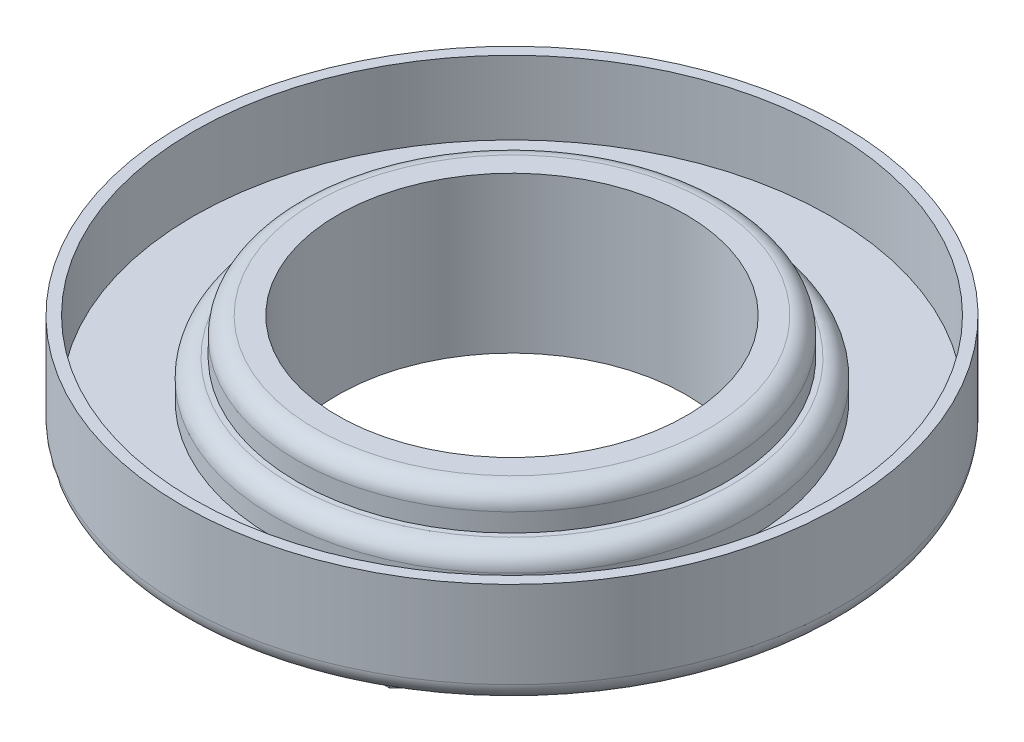
SolidWorks part; units mm, degrees
material "Zinc AC41A Alloy, As Cast"
ref_plane "Front Plane" through (0, 0, 0) normal (0, 0, 1) x (1, 0, 0)
ref_plane "Top Plane" through (0, 0, 0) normal (0, 1, 0) x (1, 0, 0)
ref_plane "Right Plane" through (0, 0, 0) normal (1, 0, 0) x (0, 0, -1)
sketch "Sketch1" plane through (0, 0, 0) normal (0, 1, 0) x (1, 0, 0)
  line L0 (0, 15.8115) -> (0, -15.8115) construction
  line L1 (-7.3398, 15.8115) -> (7.3398, 15.8115)
  line L2 (7.3398, 15.8115) -> (15.8115, 6.35)
  line L3 (15.8115, 6.35) -> (15.8115, -6.35)
  line L4 (15.8115, -6.35) -> (7.3398, -15.8115)
  line L5 (7.3398, -15.8115) -> (-7.3398, -15.8115)
  line L6 (-15.8115, -6.35) -> (-7.3398, -15.8115)
  line L7 (-15.8115, 6.35) -> (-15.8115, -6.35)
  line L8 (-7.3398, 15.8115) -> (-15.8115, 6.35)
  point P2 (0, 0)
  point P3 (15.8115, 0)
  dimension "D1" = 31.623
  dimension "D2" = 12.7
  dimension "D3" = 12.7
  dimension "D4" = 12.7
  dimension "D5" = 31.623
extrude "Boss-Extrude1" add sketch "Sketch1" along normal blind 10.795
ref_plane "Plane1" through (0, 3.5052, 0) normal (0, -1, 0) x (-1, 0, 0)
sketch "Sketch2" plane through (0, 3.5052, 0) normal (0, -1, 0) x (-1, 0, 0)
  circle A0 centre (0, 0) radius 22.8346
  dimension "D1" = 45.6692
extrude "Boss-Extrude2" add sketch "Sketch2" against normal up to vertex (7.2898 mm away)
sketch "Sketch3" plane through (0, 10.795, 0) normal (0, 1, 0) x (1, 0, 0)
  circle A0 centre (0, 0) radius 22.0726
  circle A1 centre (0, 0) radius 22.8346 construction
  circle A2 centre (0, 0) radius 16.51
  dimension "D1" = 0.762
  dimension "D2" = 33.02
extrude "Cut-Extrude1" cut sketch "Sketch3" against normal blind 5.08
sketch "Sketch4" plane through (0, 0, 0) normal (0, -1, 0) x (1, 0, 0)
  circle A0 centre (0, 0) radius 12.065
  dimension "D1" = 24.13
extrude "Cut-Extrude2" cut sketch "Sketch4" against normal through all
sketch "Sketch5" plane through (0, 10.795, 0) normal (0, 1, 0) x (1, 0, 0)
  circle A0 centre (0, 0) radius 18.1356
  circle A1 centre (0, 0) radius 16.51 construction
  circle A2 centre (0, 0) radius 16.51 construction
  circle A3 centre (0, 0) radius 14.8844
  point P3 (0, -16.51)
  point P4 (0, -18.1356)
  point P9 (0, -14.8844)
  dimension "D1" = 1.6256
  dimension "D2" = 1.6256
extrude "Cut-Extrude5" cut sketch "Sketch5" against normal blind 2.54
fillet "Fillet1" radius 1.27 1 edges at (0, 10.795, 14.8844)
fillet "Fillet2" radius 1.27 1 edges at (0, 8.255, 16.51)
fillet "Fillet3" radius 1.27 1 edges at (0, 3.5052, -22.8346)
